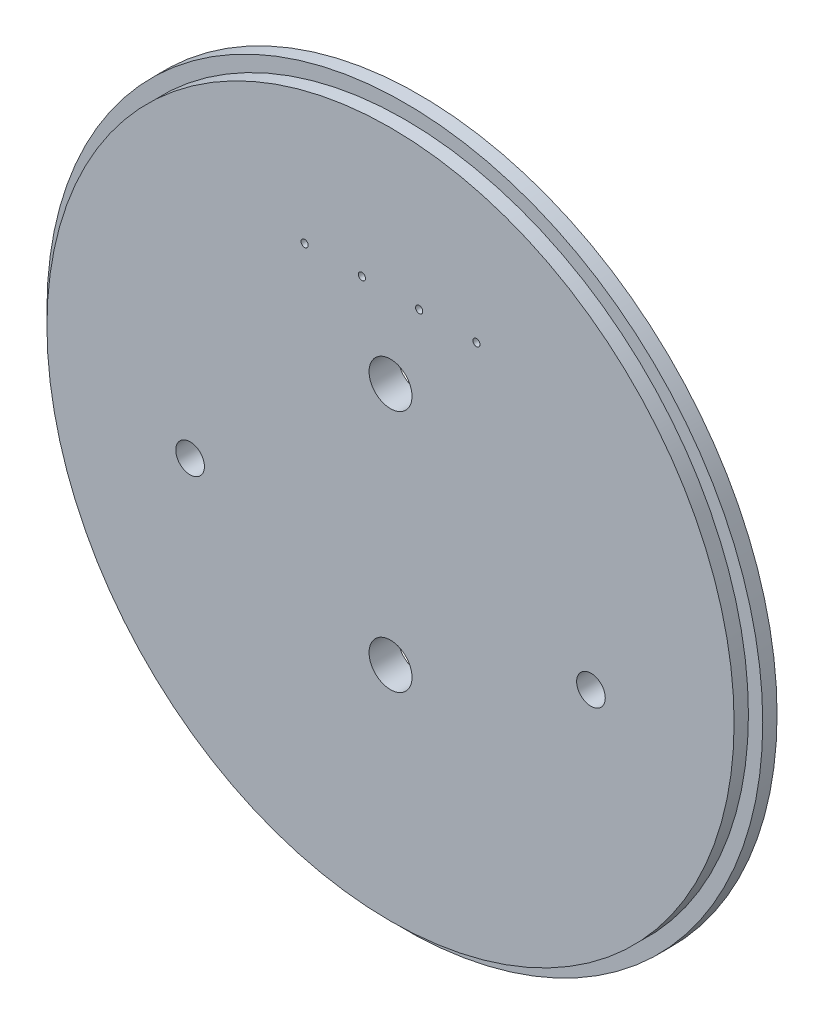
SolidWorks part; units mm, degrees
ref_plane "Front Plane" through (0, 0, 0) normal (0, 0, 1) x (1, 0, 0)
ref_plane "Top Plane" through (0, 0, 0) normal (0, 1, 0) x (1, 0, 0)
ref_plane "Right Plane" through (0, 0, 0) normal (1, 0, 0) x (0, 0, -1)
sketch "Sketch1" plane through (0, 0, 0) normal (0, 0, 1) x (1, 0, 0)
  circle A0 centre (0, 0) radius 79.375
  dimension "D1" = 158.75
extrude "Boss-Extrude1" add sketch "Sketch1" along normal blind 3.175
sketch "Sketch2" plane through (0, 0, 3.175) normal (0, 0, 1) x (1, 0, 0)
  circle A0 centre (0, 0) radius 76.2
  dimension "D1" = 152.4
extrude "Boss-Extrude2" add sketch "Sketch2" along normal blind 3.175
sketch "Sketch4" plane through (0, 0, 6.35) normal (0, 0, 1) x (1, 0, 0)
  line L0 (0, -9.525) -> (44.45, -9.525) construction
  line L1 (0, -9.525) -> (-44.45, -9.525) construction
  point P1 (-44.45, -9.525)
  point P3 (44.45, -9.525)
  dimension "D1" = 88.9
  dimension "D2" = 9.525
hole_wizard "1/4 (0.25) Diameter Hole1" positions "Sketch7" profile "Sketch9" hole size "1/4" standard "ANSI Inch" end condition through all
sketch "Sketch7" plane through (0, 0, 6.35) normal (0, 0, 1) x (1, 0, 0)
  point P0 (-44.45, -9.525)
  point P3 (44.45, -9.525)
sketch "Sketch9" plane through (-44.45, -9.525, 6.35) normal (1, 0, 0) x (0, -1, 0)
  line L0 (0, 0) -> (0, 6.35)
  line L1 (0, 6.35) -> (3.175, 6.35)
  line L2 (3.175, 6.35) -> (3.175, 0)
  line L5 (3.175, 0) -> (0, 0)
  line L11 (0, -6.35) -> (0, 107.95) construction
  dimension "Thru Hole Dia." = 6.35
  dimension "Thru Hole Depth" = 6.35
sketch "Sketch11" plane through (0, 0, 6.35) normal (0, 0, 1) x (1, 0, 0)
  line L0 (-19.05, 44.45) -> (19.05, 44.45) construction
  point P2 (0, 44.45)
  point P5 (-19.05, 44.45)
  point P7 (-6.35, 44.45)
  point P8 (6.35, 44.45)
  point P9 (19.05, 44.45)
  dimension "D1" = 38.1
  dimension "D2" = 44.45
  dimension "D3" = 4
hole_wizard "1/16 (0.0625) Diameter Hole1" positions "Sketch12" profile "Sketch13" hole size "1/16" standard "ANSI Inch" end condition through all
sketch "Sketch12" plane through (0, 0, 6.35) normal (0, 0, 1) x (1, 0, 0)
  point P0 (-19.05, 44.45)
  point P3 (-6.35, 44.45)
  point P6 (6.35, 44.45)
  point P9 (19.05, 44.45)
sketch "Sketch13" plane through (-19.05, 44.45, 6.35) normal (1, 0, 0) x (0, -1, 0)
  line L0 (0, 0) -> (0, 6.35)
  line L1 (0, 6.35) -> (0.7937, 6.35)
  line L2 (0.7937, 6.35) -> (0.7937, 0)
  line L5 (0.7937, 0) -> (0, 0)
  line L11 (0, -6.35) -> (0, 107.95) construction
  dimension "Thru Hole Dia." = 1.5875
  dimension "Thru Hole Depth" = 6.35
sketch "Sketch14" plane through (0, 0, 6.35) normal (0, 0, 1) x (1, 0, 0)
  line L0 (0, -26.9875) -> (0, 26.9875)
  point P4 (0, 0)
  dimension "D1" = 53.975
hole_wizard "3/8 (0.375) Diameter Hole1" positions "Sketch15" profile "Sketch16" hole size "3/8" standard "ANSI Inch" end condition through all
sketch "Sketch15" plane through (0, 0, 6.35) normal (0, 0, 1) x (1, 0, 0)
  point P0 (0, -26.9875)
  point P3 (0, 26.9875)
sketch "Sketch16" plane through (0, -26.9875, 6.35) normal (1, 0, 0) x (0, -1, 0)
  line L0 (0, 0) -> (0, 6.35)
  line L1 (0, 6.35) -> (4.7625, 6.35)
  line L2 (4.7625, 6.35) -> (4.7625, 0)
  line L5 (4.7625, 0) -> (0, 0)
  line L11 (0, -6.35) -> (0, 107.95) construction
  dimension "Thru Hole Dia." = 9.525
  dimension "Thru Hole Depth" = 6.35
